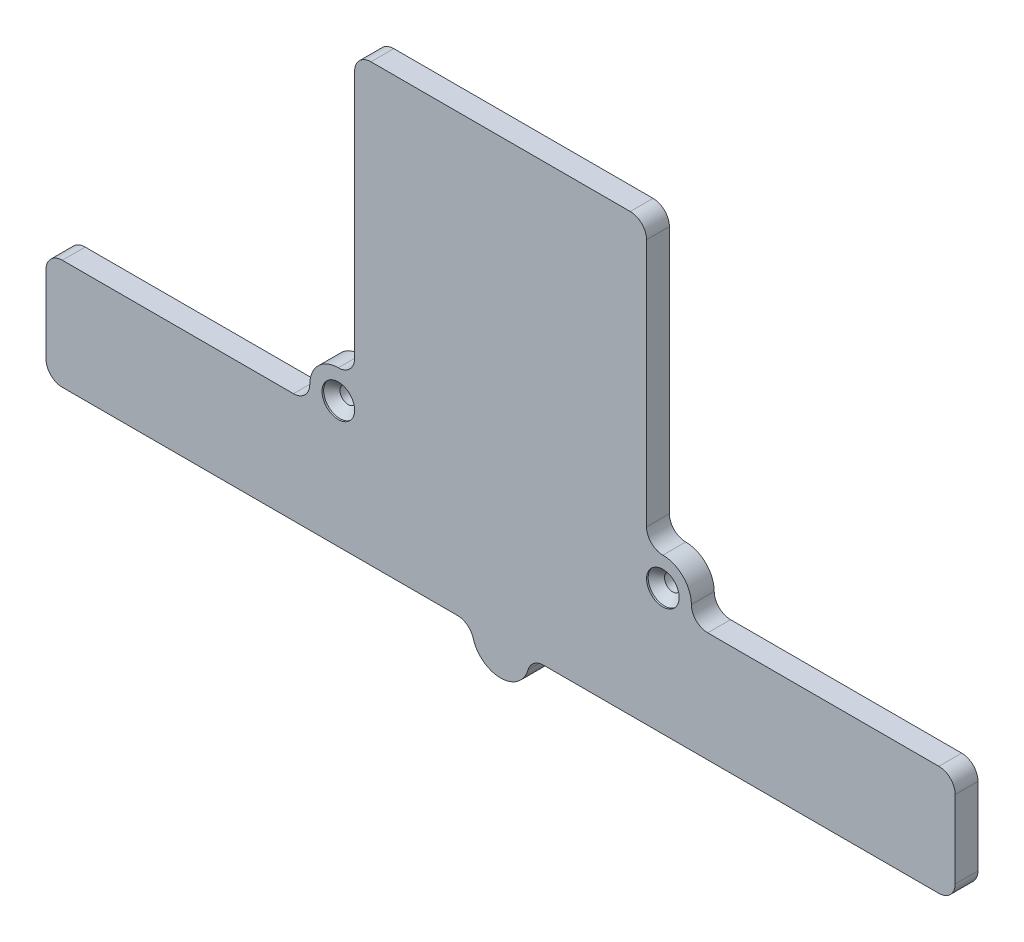
SolidWorks part; units mm, degrees
ref_plane "Front Plane" through (0, 0, 0) normal (0, 0, 1) x (1, 0, 0)
ref_plane "Top Plane" through (0, 0, 0) normal (0, 1, 0) x (1, 0, 0)
ref_plane "Right Plane" through (0, 0, 0) normal (1, 0, 0) x (0, 0, -1)
sketch "Sketch1" plane through (0, 0, 0) normal (0, 0, 1) x (1, 0, 0)
  line L8 (-53.75, -26.75) -> (-5.2915, -26.75)
  line L9 (55.75, -24.75) -> (55.75, -15.25)
  line L10 (53.75, -13.25) -> (25.4, -13.25)
  line L11 (17.9, -5.75) -> (17.9, 24.75)
  line L12 (15.9, 26.75) -> (-15.9, 26.75)
  line L13 (-17.9, 24.75) -> (-17.9, -5.75)
  line L14 (-25.4, -13.25) -> (-53.75, -13.25)
  line L15 (-55.75, -15.25) -> (-55.75, -24.75)
  line L16 (-53.75, -26.75) -> (-5.2915, -26.75)
  line L17 (55.75, -24.75) -> (55.75, -15.25)
  line L18 (53.75, -13.25) -> (25.4, -13.25)
  line L19 (17.9, -5.75) -> (17.9, 24.75)
  line L20 (15.9, 26.75) -> (-15.9, 26.75)
  line L21 (-17.9, 24.75) -> (-17.9, -5.75)
  line L22 (-25.4, -13.25) -> (-53.75, -13.25)
  line L23 (-55.75, -15.25) -> (-55.75, -24.75)
  line L66 (5.2915, -26.75) -> (53.75, -26.75)
  line L67 (5.2915, -26.75) -> (53.75, -26.75)
  arc A12 (53.75, -26.75) -> (55.75, -24.75) centre (53.75, -24.75) ccw
  arc A13 (55.75, -15.25) -> (53.75, -13.25) centre (53.75, -15.25) ccw
  arc A14 (23.4, -11.25) -> (25.4, -13.25) centre (25.4, -11.25) ccw
  arc A15 (23.4, -11.25) -> (19.9, -7.75) centre (19.9, -11.25) ccw
  arc A16 (17.9, -5.75) -> (19.9, -7.75) centre (19.9, -5.75) ccw
  arc A17 (17.9, 24.75) -> (15.9, 26.75) centre (15.9, 24.75) ccw
  arc A18 (-15.9, 26.75) -> (-17.9, 24.75) centre (-15.9, 24.75) ccw
  arc A19 (-19.9, -7.75) -> (-17.9, -5.75) centre (-19.9, -5.75) ccw
  arc A20 (-19.9, -7.75) -> (-23.4, -11.25) centre (-19.9, -11.25) ccw
  arc A21 (-25.4, -13.25) -> (-23.4, -11.25) centre (-25.4, -11.25) ccw
  arc A22 (-53.75, -13.25) -> (-55.75, -15.25) centre (-53.75, -15.25) ccw
  arc A23 (-55.75, -24.75) -> (-53.75, -26.75) centre (-53.75, -24.75) ccw
  arc A24 (53.75, -26.75) -> (55.75, -24.75) centre (53.75, -24.75) ccw
  arc A25 (55.75, -15.25) -> (53.75, -13.25) centre (53.75, -15.25) ccw
  arc A26 (23.4, -11.25) -> (25.4, -13.25) centre (25.4, -11.25) ccw
  arc A27 (23.4, -11.25) -> (19.9, -7.75) centre (19.9, -11.25) ccw
  arc A28 (17.9, -5.75) -> (19.9, -7.75) centre (19.9, -5.75) ccw
  arc A29 (17.9, 24.75) -> (15.9, 26.75) centre (15.9, 24.75) ccw
  arc A30 (-15.9, 26.75) -> (-17.9, 24.75) centre (-15.9, 24.75) ccw
  arc A31 (-19.9, -7.75) -> (-17.9, -5.75) centre (-19.9, -5.75) ccw
  arc A32 (-19.9, -7.75) -> (-23.4, -11.25) centre (-19.9, -11.25) ccw
  arc A33 (-25.4, -13.25) -> (-23.4, -11.25) centre (-25.4, -11.25) ccw
  arc A34 (-53.75, -13.25) -> (-55.75, -15.25) centre (-53.75, -15.25) ccw
  arc A35 (-55.75, -24.75) -> (-53.75, -26.75) centre (-53.75, -24.75) ccw
  arc A100 (-3.3673, -28.2045) -> (-5.2915, -26.75) centre (-5.2915, -28.75) ccw
  arc A101 (-3.3673, -28.2045) -> (-5.2915, -26.75) centre (-5.2915, -28.75) ccw
  arc A102 (-3.3673, -28.2045) -> (3.3673, -28.2045) centre (0, -27.25) ccw
  arc A103 (-3.3673, -28.2045) -> (3.3673, -28.2045) centre (0, -27.25) ccw
  arc A104 (5.2915, -26.75) -> (3.3673, -28.2045) centre (5.2915, -28.75) ccw
  arc A105 (5.2915, -26.75) -> (3.3673, -28.2045) centre (5.2915, -28.75) ccw
  dimension "D1" = 0
extrude "Boss-Extrude1" add sketch "Sketch1" along normal blind 2.8
sketch "Sketch3" plane through (0, 0, 2.8) normal (0, 0, 1) x (1, 0, 0)
  line L0 (0, 32.8811) -> (0, -41.8665) construction
  circle A0 centre (-19.9, -11.25) radius 1
  arc A1 (-19.9, -7.75) -> (-23.4, -11.25) centre (-19.9, -11.25) ccw construction
  circle A2 centre (19.9, -11.25) radius 1
  dimension "D1" = 2
extrude "Cut-Extrude1" cut sketch "Sketch3" against normal up to next
hole_wizard "CSK for M2 Flat Head Machine Screw1" positions "Sketch5" profile "Sketch4" countersink size "M2" standard "ANSI Metric" end condition through all
sketch "Sketch5" plane through (0, 0, 2.8) normal (0, 0, 1) x (1, 0, 0)
  point P0 (-19.9, -11.25)
  point P3 (19.9, -11.25)
sketch "Sketch4" plane through (-19.9, -11.25, 2.8) normal (1, 0, 0) x (0, -1, 0)
  line L0 (0, 0) -> (0, 2.8)
  line L1 (0, 2.8) -> (1, 2.8)
  line L2 (1, 2.8) -> (1, 1.2)
  line L3 (1, 1.2) -> (2, 0.2)
  line L4 (2, 0.2) -> (2, 0)
  line L6 (2, 0) -> (0, 0)
  line L7 (-1, 1.2) -> (-2, 0.2) construction
  line L11 (0, -6.35) -> (0, 107.95) construction
  dimension "Thru Hole Dia." = 2
  dimension "Thru Hole Depth" = 2.8
  dimension "C'Sink Dia." = 4
  dimension "C'Sink Angle" = 90
  dimension "Head Clearance" = 0.2
ref_plane "Plane1" through (0, 0, 2.8) normal (0, 0, 1) x (1, 0, 0)
sketch "Sketch6" plane through (0, 0, 2.8) normal (0, 0, 1) x (1, 0, 0)
  line L0 (0, -30.75) -> (55.75, -30.75) construction
  line L1 (55.75, -30.75) -> (55.75, -24.75) construction
  line L2 (-17.9, 24.75) -> (-17.9, 26.75) construction
  line L3 (-17.9, 26.75) -> (-15.9, 26.75) construction
  arc A0 (-3.3673, -28.2045) -> (3.3673, -28.2045) centre (0, -27.25) ccw construction
  point P8 (55.75, -30.75)
  point P14 (-17.9, 26.75)
